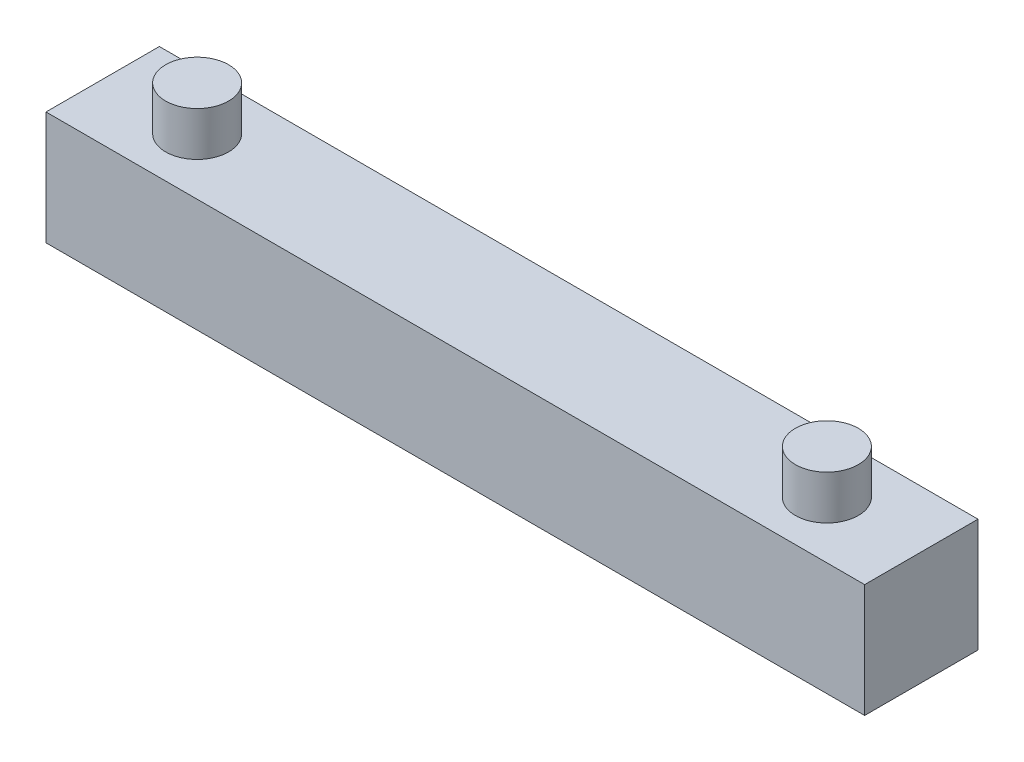
SolidWorks part; units mm, degrees
ref_plane "Front Plane" through (0, 0, 0) normal (0, 0, 1) x (1, 0, 0)
ref_plane "Top Plane" through (0, 0, 0) normal (0, 1, 0) x (1, 0, 0)
ref_plane "Right Plane" through (0, 0, 0) normal (1, 0, 0) x (0, 0, -1)
sketch "Sketch3" plane through (0, 0, 0) normal (0, 0, 1) x (1, 0, 0)
  line L1 (0, 0) -> (65, 0)
  line L2 (0, 0) -> (0, 9)
  line L3 (0, 9) -> (65, 9)
  line L4 (65, 0) -> (65, 9)
  dimension "D1" = 65
  dimension "D2" = 9
extrude "Boss-Extrude2" add sketch "Sketch3" along normal blind 9
sketch "Sketch4" plane through (0, 9, 0) normal (0, 1, 0) x (1, 0, 0)
  circle A0 centre (57.5, -4.5) radius 2.5
  circle A1 centre (7.5, -4.5) radius 2.5
  dimension "D1" = 5
extrude "Boss-Extrude3" add sketch "Sketch4" along normal blind 3.5
